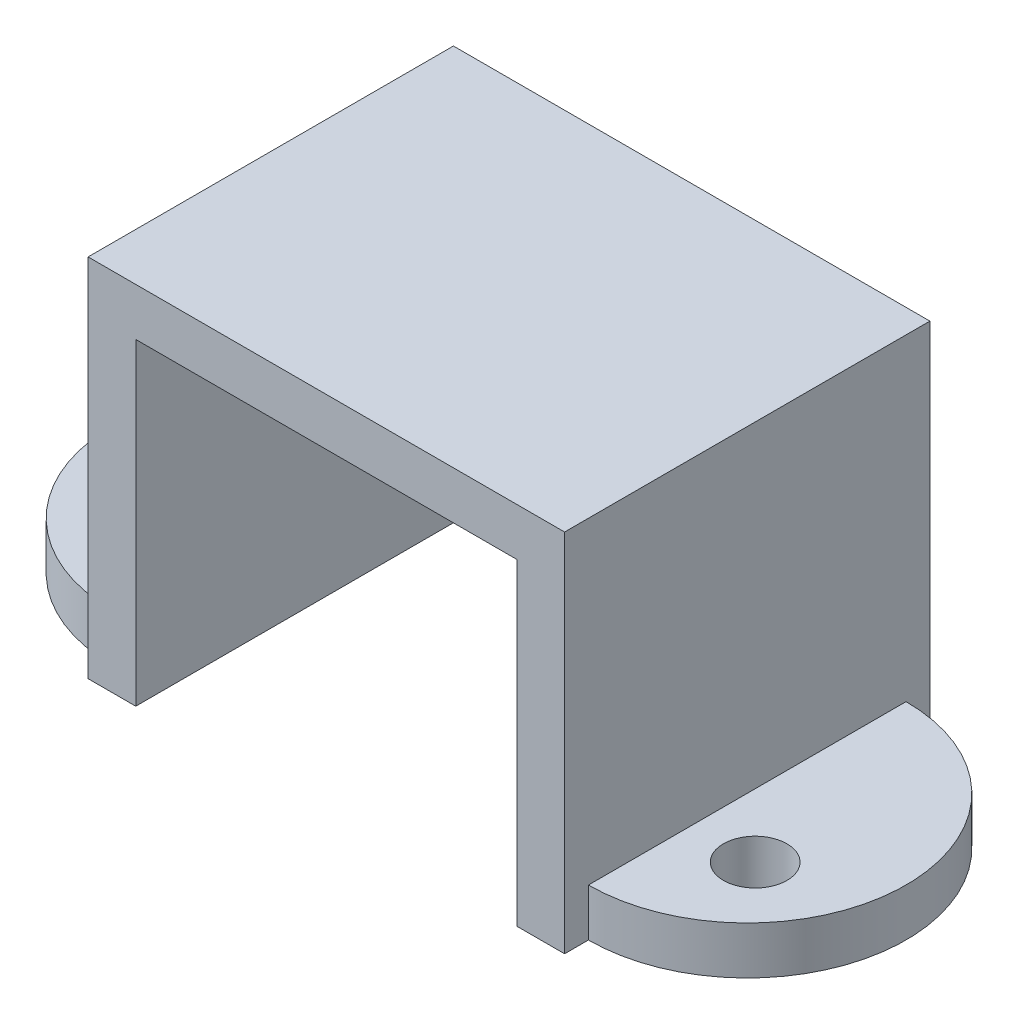
SolidWorks part; units mm, degrees
ref_plane "Front Plane" through (0, 0, 0) normal (0, 0, 1) x (1, 0, 0)
ref_plane "Top Plane" through (0, 0, 0) normal (0, 1, 0) x (1, 0, 0)
ref_plane "Right Plane" through (0, 0, 0) normal (1, 0, 0) x (0, 0, -1)
sketch "Sketch1" plane through (0, 0, 0) normal (0, 0, 1) x (1, 0, 0)
  line L1 (-7.5, 5.75) -> (7.5, 5.75)
  line L2 (-7.5, 5.75) -> (-7.5, -5.75)
  line L3 (-7.5, -5.75) -> (7.5, -5.75)
  line L4 (7.5, 5.75) -> (7.5, -5.75)
  line L5 (-7.5, 5.75) -> (7.5, -5.75) construction
  line L6 (-7.5, -5.75) -> (7.5, 5.75) construction
  line L7 (-6, -5.75) -> (6, -5.75) construction
  line L8 (-6, -5.75) -> (-6, 4.25)
  line L9 (-6, 4.25) -> (6, 4.25)
  line L10 (6, -5.75) -> (6, 4.25)
  point P0 (0, 0)
  point P10 (0, 4.25)
  point P11 (0, 5.75)
  dimension "D1" = 15
  dimension "D2" = 11.5
  dimension "D3" = 12
  dimension "D4" = 10
extrude "Boss-Extrude1" add sketch "Sketch1" against normal blind 11.5 contours L10 L3 L4 L1 L2 L8 L9
sketch "Sketch2" plane through (0, -5.75, 0) normal (0, -1, 0) x (1, 0, 0)
  line L0 (-7.5, -11.5) -> (-7.5, 0) construction
  line L1 (-7.5, -0.75) -> (-7.5, -10.75)
  line L2 (-7.5, -0.75) -> (-7.5, -10.75)
  line L3 (0, 0) -> (0, -11.5) construction
  line L4 (-6, -11.5) -> (6, -11.5) construction
  line L5 (7.5, -0.75) -> (7.5, -10.75)
  line L6 (7.5, -0.75) -> (7.5, -10.75)
  line L7 (-7.5, 0) -> (-6, 0) construction
  arc A0 (-7.5, -10.75) -> (-7.5, -0.75) centre (-7.5, -5.75) cw
  circle A1 centre (-9.5, -4) radius 1
  circle A2 centre (9.5, -4) radius 1
  arc A3 (7.5, -10.75) -> (7.5, -0.75) centre (7.5, -5.75) ccw
  point P17 (0, 0)
  line M6 (-7.5, 0) -> (-7.5, -11.5)
  dimension "D1" = 5
  dimension "D3" = 2
  dimension "D2" = 2
  dimension "D4" = 4
extrude "Boss-Extrude2" add sketch "Sketch2" against normal blind 1.5 contours A0 A1 M6 | L5 A3 A2
